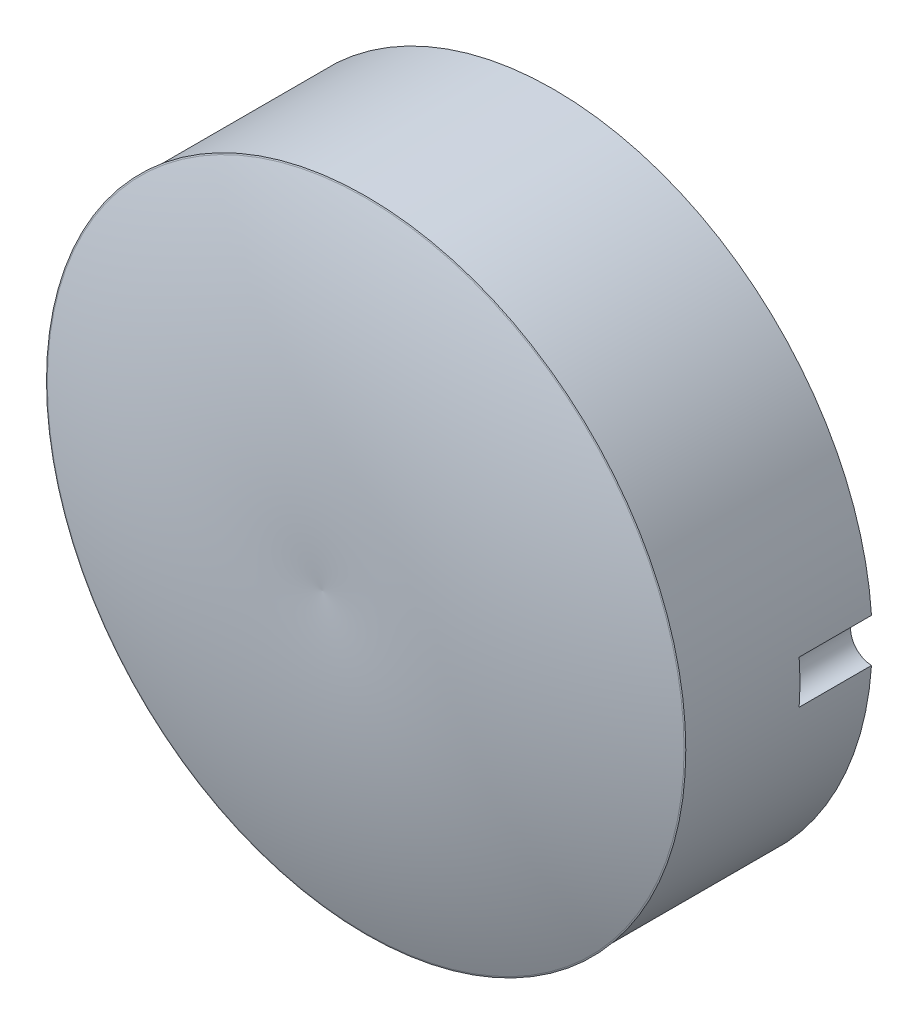
SolidWorks part; units mm, degrees
ref_plane "Front Plane" through (0, 0, 0) normal (0, 0, 1) x (1, 0, 0)
ref_plane "Top Plane" through (0, 0, 0) normal (0, 1, 0) x (1, 0, 0)
ref_plane "Right Plane" through (0, 0, 0) normal (1, 0, 0) x (0, 0, -1)
sketch "Sketch1" plane through (0, 0, 0) normal (0, 0, 1) x (1, 0, 0)
  circle A0 centre (0, 0) radius 22
  dimension "D1" = 44
extrude "Boss-Extrude1" add sketch "Sketch1" along normal blind 13
sketch "Sketch2" plane through (0, 0, 13) normal (0, 0, 1) x (1, 0, 0)
  line L0 (0, 0) -> (22, 0)
  circle A0 centre (0, 0) radius 22 construction
sketch "Sketch3" plane through (0, 0, 0) normal (0, 1, 0) x (1, 0, 0)
  line L1 (0, 0) -> (0, -23.6393) construction
  line L2 (0, -16) -> (0, -13)
  line L3 (22.0868, -12.97) -> (0, -13)
  line L4 (22, -13) -> (22.0868, -12.97)
  arc A0 (22, -13) -> (0, -16) centre (4.1432, 35.7832) cw
  point P2 (0, -14.5)
revolve "Revolve2" add sketch "Sketch3" angle 360 about L1
sketch "Sketch4" plane through (0, 0, 0) normal (0, 0, -1) x (-1, 0, 0)
  circle A0 centre (-22, 0) radius 1.5
  dimension "D1" = 3
extrude "Cut-Extrude1" cut sketch "Sketch4" against normal blind 5
